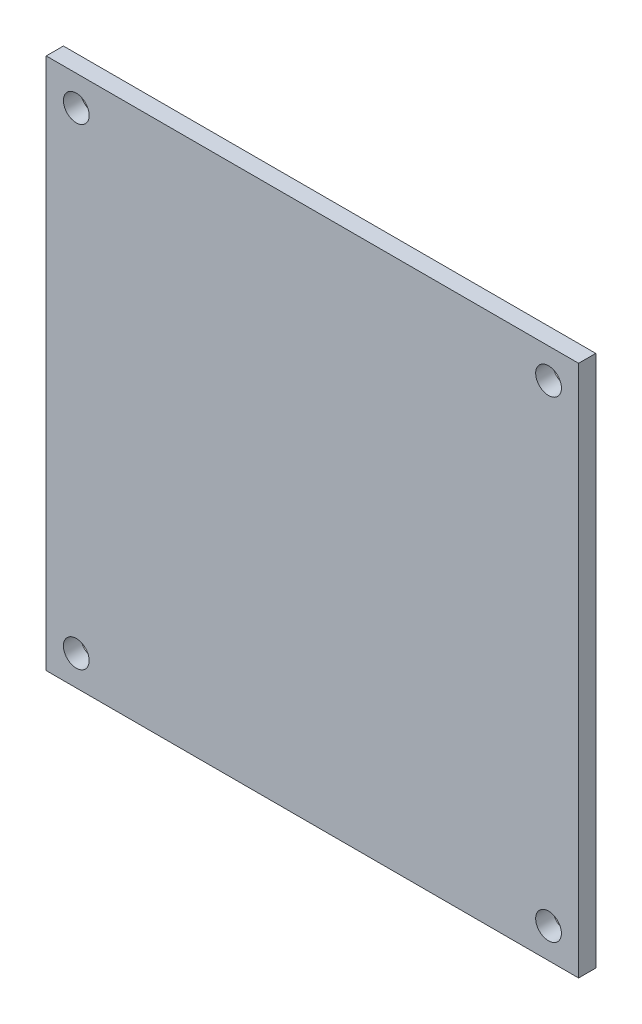
SolidWorks part; units mm, degrees
ref_plane "Alzado" through (0, 0, 0) normal (0, 0, 1) x (1, 0, 0)
ref_plane "Planta" through (0, 0, 0) normal (0, 1, 0) x (1, 0, 0)
ref_plane "Vista lateral" through (0, 0, 0) normal (1, 0, 0) x (0, 0, -1)
sketch "Croquis1" plane through (0, 0, 0) normal (0, 0, 1) x (1, 0, 0)
  line L1 (-89.1419, 30.4888) -> (-27.1419, 30.4888)
  line L2 (-89.1419, 30.4888) -> (-89.1419, -31.5112)
  line L3 (-89.1419, -31.5112) -> (-27.1419, -31.5112)
  line L4 (-27.1419, 30.4888) -> (-27.1419, -31.5112)
  circle A0 centre (-85.6419, 26.9888) radius 1.5
  circle A1 centre (-30.6419, 26.9888) radius 1.5
  circle A2 centre (-30.6419, -28.0112) radius 1.5
  circle A3 centre (-85.6419, -28.0112) radius 1.5
  dimension "D3" = 3.5
  dimension "D1" = 62
  dimension "D2" = 62
  dimension "D4" = 3.5
  dimension "D5" = 2
  dimension "D6" = 2
extrude "Saliente-Extruir1" add sketch "Croquis1" along normal blind 2
sketch "Croquis2" plane through (0, 0, 0) normal (0, 0, -1) x (-1, 0, 0)
  line L0 (89.1419, 30.4888) -> (89.1419, -31.5112) construction
  line L1 (84.1419, -12.0112) -> (78.1419, -12.0112)
  line L2 (84.1419, -12.0112) -> (84.1419, 10.9888)
  line L3 (84.1419, 10.9888) -> (78.1419, 10.9888)
  line L4 (78.1419, -12.0112) -> (78.1419, 10.9888)
  line L5 (89.1419, -31.5112) -> (27.1419, -31.5112) construction
  line L8 (82.1419, -10.7612) -> (80.1419, -10.7612)
  line L9 (82.1419, -10.7612) -> (82.1419, 9.7388)
  line L10 (82.1419, 9.7388) -> (80.1419, 9.7388)
  line L11 (80.1419, -10.7612) -> (80.1419, 9.7388)
  dimension "D1" = 6
  dimension "D2" = 23
  dimension "D3" = 5
  dimension "D4" = 19.5
  dimension "D5" = 2
  dimension "D6" = 20.5
  dimension "D7" = 1.25
  dimension "D8" = 2
extrude "Saliente-Extruir2" add sketch "Croquis2" along normal blind 10
